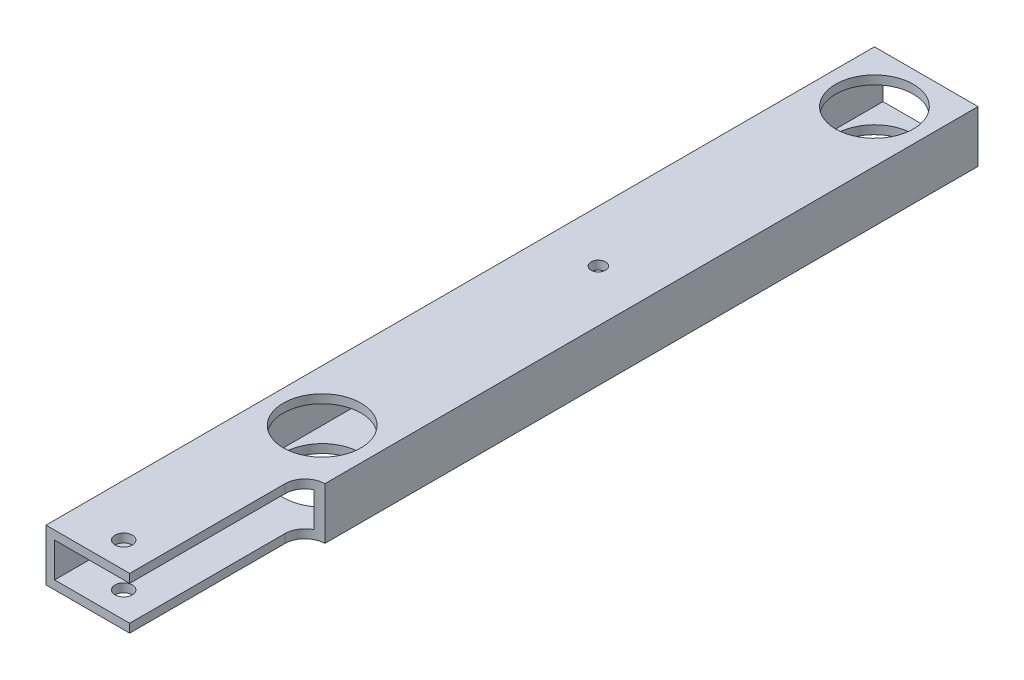
SolidWorks part; units mm, degrees
material "6063-T6"
ref_plane "Front" through (0, 0, 0) normal (0, 0, 1) x (1, 0, 0)
ref_plane "Top" through (0, 0, 0) normal (0, 1, 0) x (1, 0, 0)
ref_plane "Right" through (0, 0, 0) normal (1, 0, 0) x (0, 0, -1)
sketch "Sketch1" plane through (0, 0, 0) normal (0, 0, 1) x (1, 0, 0)
  line L0 (3.175, 3.175) -> (34.925, 3.175)
  line L1 (0, 0) -> (38.1, 0)
  line L2 (0, 0) -> (0, 19.05)
  line L3 (0, 19.05) -> (38.1, 19.05)
  line L4 (38.1, 0) -> (38.1, 19.05)
  line L5 (34.925, 3.175) -> (34.925, 15.875)
  line L6 (3.175, 15.875) -> (34.925, 15.875)
  line L7 (3.175, 3.175) -> (3.175, 15.875)
  dimension "D1" = 19.05
  dimension "D2" = 38.1
  dimension "D3" = 3.175
extrude "Boss-Extrude1" add sketch "Sketch1" along normal blind 304.8
sketch "Sketch2" plane through (0, 19.05, 0) normal (0, 1, 0) x (1, 0, 0)
  line L0 (19.05, 0) -> (19.05, -19.05) construction
  line L2 (19.05, -19.05) -> (19.05, -222.25) construction
  line L4 (38.1, -304.8) -> (38.1, 0) construction
  line L5 (38.1, 0) -> (0, 0) construction
  circle A0 centre (19.05, -19.05) radius 14.2875
  circle A1 centre (19.05, -222.25) radius 14.2875
  dimension "D1" = 28.575
  dimension "D4" = 28.575
  dimension "D2" = 19.05
  dimension "D3" = 203.2
  dimension "D5" = 19.05
extrude "Cut-Extrude1" cut sketch "Sketch2" against normal through all
sketch "Sketch3" plane through (0, 19.05, 0) normal (0, 1, 0) x (1, 0, 0)
  line L0 (19.05, -295.275) -> (19.05, -304.8) construction
  line L1 (38.1, -304.8) -> (0, -304.8) construction
  circle A0 centre (19.05, -295.275) radius 3.175
  dimension "D1" = 6.35
  dimension "D2" = 9.525
extrude "Cut-Extrude2" cut sketch "Sketch3" against normal through all
sketch "Sketch4" plane through (0, 19.05, 0) normal (0, 1, 0) x (1, 0, 0)
  line L0 (30.7745, -304.8) -> (30.7745, -247.65)
  line L1 (38.1, -304.8) -> (0, -304.8) construction
  line L2 (38.1, -240.3245) -> (38.1, -304.8)
  line L3 (38.1, -304.8) -> (38.1, 0) construction
  line L4 (38.1, -304.8) -> (30.7745, -304.8)
  arc A0 (38.1, -240.3245) -> (30.7745, -247.65) centre (38.1, -247.65) ccw
  dimension "D1" = 57.15
extrude "Cut-Extrude3" cut sketch "Sketch4" against normal through all
sketch "Sketch5" plane through (0, 19.05, 0) normal (0, 1, 0) x (1, 0, 0)
  circle A0 centre (19.05, -120.65) radius 2.667 construction
  circle A1 centre (19.05, -120.65) radius 2.667
extrude "Cut-Extrude4" cut sketch "Sketch5" against normal through all
sketch "Sketch6" plane through (0, 0, 0) normal (0, -1, 0) x (1, 0, 0)
  circle A0 centre (19.05, 120.65) radius 6.35
  dimension "D1" = 12.7
extrude "Cut-Extrude5" cut sketch "Sketch6" against normal up to next
